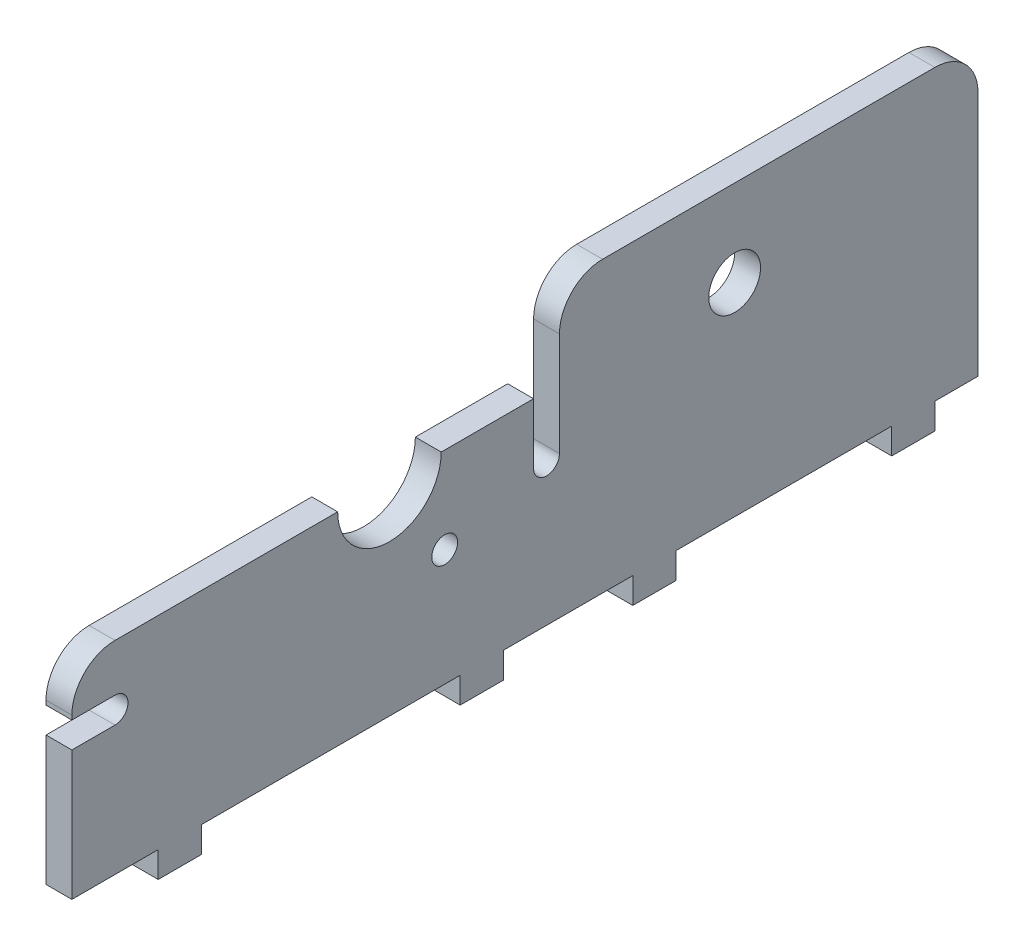
SolidWorks part; units mm, degrees
ref_plane "Front Plane" through (0, 0, 0) normal (0, 0, 1) x (1, 0, 0)
ref_plane "Top Plane" through (0, 0, 0) normal (0, 1, 0) x (1, 0, 0)
ref_plane "Right Plane" through (0, 0, 0) normal (1, 0, 0) x (0, 0, -1)
sketch "Sketch1" plane through (0, 0, 0) normal (1, 0, 0) x (0, 0, -1)
  line L0 (0, 55) -> (0, -55) construction
  line L1 (75, 0) -> (-30, 0)
  line L2 (75, 0) -> (75, 23.5)
  line L3 (75, 23.5) -> (-30, 23.5)
  line L4 (-30, 0) -> (-30, 23.5)
  line L5 (55, 0) -> (-55, 0) construction
  point P0 (0, 0)
  dimension "D2" = 30
  dimension "D1" = 105
  dimension "D4" = 23.5
extrude "Boss-Extrude1" add sketch "Sketch1" along normal blind 3
sketch "Sketch2" plane through (3, 0, 0) normal (1, 0, 0) x (0, 0, -1)
  line L0 (-30, 0) -> (75, 0) construction
  line L1 (-30, 23.5) -> (-30, 0) construction
  line L6 (55, 0) -> (-55, 0) construction
  line L7 (-26.9862, 0) -> (-28.4862, -10) construction
  circle A0 centre (6.8, 23.5) radius 6
  circle A1 centre (13.2, 13.5) radius 1.5
  point P6 (-28.4862, -10)
  point P11 (28.0724, -10)
  dimension "D1" = 12
  dimension "D3" = 6.8
  dimension "D4" = 3
  dimension "D2" = 23.5
  dimension "D5" = 43.2
  dimension "D6" = 13.5
extrude "Cut-Extrude1" cut sketch "Sketch2" against normal through all
sketch "Sketch3" plane through (3, 0, 0) normal (1, 0, 0) x (0, 0, -1)
  line L0 (-30, 23.5) -> (-30, 0) construction
  line L1 (-25, 15) -> (-30, 15)
  line L3 (-25, 18) -> (-30, 18)
  line L5 (-30, 0) -> (75, 0) construction
  line L11 (-30, 18) -> (-30, 15)
  arc A0 (-25, 15) -> (-25, 18) centre (-25, 16.5) ccw
  dimension "D1" = 1.5
  dimension "D2" = 15
extrude "Cut-Extrude2" cut sketch "Sketch3" against normal through all
ref_plane "Plane2" through (0, 22.25, 0) normal (0, -1, 0) x (-1, 0, 0)
sketch "Sketch4" plane through (0, 0, 0) normal (0, -1, 0) x (1, 0, 0)
  line L0 (3, 30) -> (3, -75) construction
  line L1 (3, 20) -> (0, 20)
  line L2 (3, 20) -> (3, 15)
  line L3 (3, 15) -> (0, 15)
  line L4 (0, 20) -> (0, 15)
  line L5 (0, 30) -> (0, -75) construction
  line L6 (3, 30) -> (0, 30) construction
  dimension "D1" = 5
  dimension "D2" = 10
extrude "Boss-Extrude2" add sketch "Sketch4" along normal blind 3
mirror "Mirror4" about plane through (0, 0, 0) normal (0, 0, 1) of "Boss-Extrude2"
sketch "Sketch5" plane through (0, 0, 0) normal (0, -1, 0) x (1, 0, 0)
  line L0 (3, -15) -> (3, -20) construction
  line L1 (0, -35) -> (3, -35)
  line L2 (0, -35) -> (0, -40)
  line L3 (0, -40) -> (3, -40)
  line L4 (3, -35) -> (3, -40)
  line L5 (0, -65) -> (3, -65)
  line L6 (0, -65) -> (0, -70)
  line L7 (0, -70) -> (3, -70)
  line L8 (3, -65) -> (3, -70)
  line L9 (0, -20) -> (0, -15) construction
  line L10 (3, -20) -> (0, -20) construction
  dimension "D1" = 5
  dimension "D2" = 5
  dimension "D3" = 15
  dimension "D4" = 25
sketch "Sketch8" plane through (3, 0, 0) normal (1, 0, 0) x (0, 0, -1)
  line L0 (23.5, 16.5) -> (23.5, 23.5)
  line L1 (75, 23.5) -> (12.8, 23.5) construction
  line L2 (23.5, 23.5) -> (26.5, 23.5)
  line L3 (26.5, 23.5) -> (26.5, 16.5)
  line L4 (1.65, 0) -> (-1.65, 0) construction
  arc A0 (23.5, 16.5) -> (26.5, 16.5) centre (25, 16.5) ccw
  arc A1 (-25, 15) -> (-25, 18) centre (-25, 16.5) ccw construction
  dimension "D1" = 3
  dimension "D2" = 50
  dimension "D3" = 16.5
extrude "Cut-Extrude4" cut sketch "Sketch8" against normal through all
extrude "Boss-Extrude3" add sketch "Sketch5" along normal blind 3
sketch "Sketch9" plane through (0, 23.5, 0) normal (0, 1, 0) x (1, 0, 0)
  line L0 (0, 75) -> (0, 26.5) construction
  line L1 (0, 26.5) -> (3, 26.5)
  line L2 (0, 26.5) -> (0, 75)
  line L3 (0, 75) -> (3, 75)
  line L4 (3, 26.5) -> (3, 75)
extrude "Boss-Extrude5" add sketch "Sketch9" along normal blind 10
sketch "Sketch10" plane through (3, 0, 0) normal (1, 0, 0) x (0, 0, -1)
  line L0 (1.65, 0) -> (-1.65, 0) construction
  line L1 (75, 0) -> (75, 33.5) construction
  circle A0 centre (46.8, 23.5) radius 3
  dimension "D1" = 6
  dimension "D2" = 23.5
  dimension "D3" = 28.2
extrude "Cut-Extrude5" cut sketch "Sketch10" against normal through all
fillet "Fillet5" radius 5 3 edges at (1.5, 33.5, -75) (1.5, 33.5, -26.5) (1.5, 23.5, 30)
